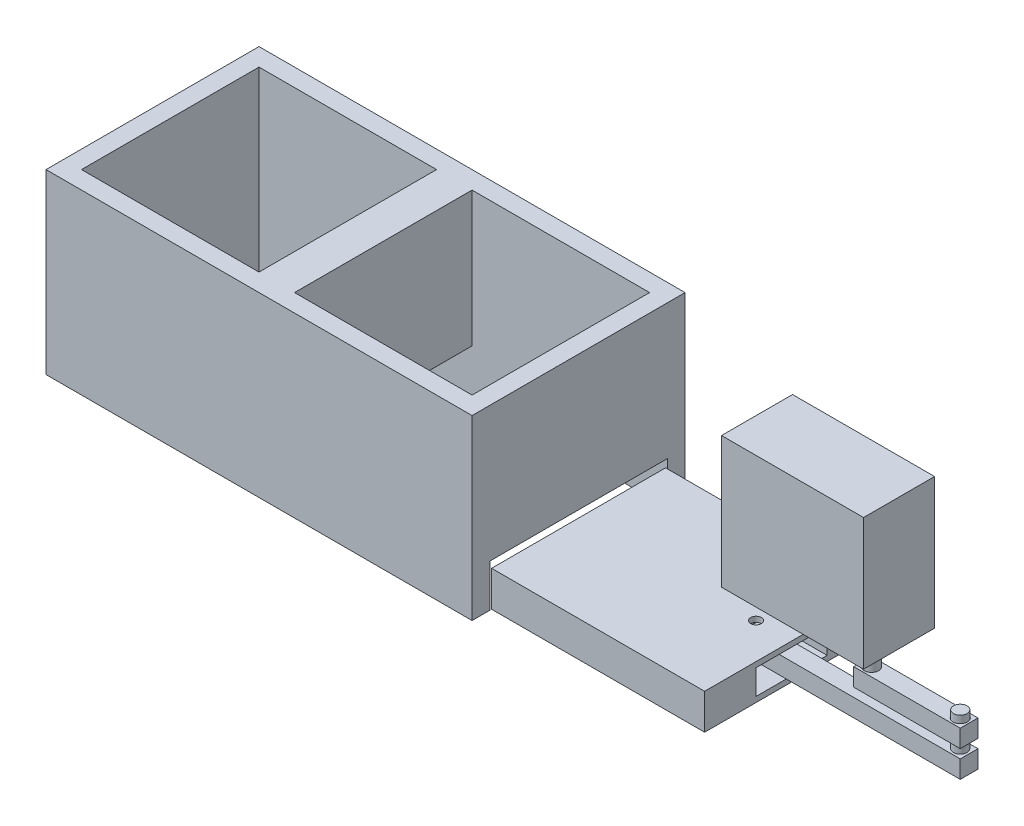
SolidWorks part; units mm, degrees
ref_plane "前视基准面" through (0, 0, 0) normal (0, 0, 1) x (1, 0, 0)
ref_plane "上视基准面" through (0, 0, 0) normal (0, 1, 0) x (1, 0, 0)
ref_plane "右视基准面" through (0, 0, 0) normal (1, 0, 0) x (0, 0, -1)
sketch "草图1" plane through (0, 0, 0) normal (0, 1, 0) x (1, 0, 0)
  line L1 (-30, 30) -> (30, 30)
  line L2 (-30, 30) -> (-30, -30)
  line L3 (-30, -30) -> (30, -30)
  line L4 (30, 30) -> (30, -30)
  dimension "D1" = 30
  dimension "D2" = 30
  dimension "D3" = 30
  dimension "D4" = 30
extrude "凸台-拉伸1" add sketch "草图1" along normal blind 50
sketch "草图2" plane through (0, 0, 0) normal (0, -1, 0) x (1, 0, 0)
  line L1 (25, 25) -> (-25, 25)
  line L2 (25, 25) -> (25, -25)
  line L3 (25, -25) -> (-25, -25)
  line L4 (-25, 25) -> (-25, -25)
  dimension "D1" = 25
  dimension "D2" = 25
  dimension "D3" = 25
  dimension "D4" = 25
extrude "切除-拉伸1" cut sketch "草图2" against normal through all
sketch "草图3" plane through (30, 0, 0) normal (1, 0, 0) x (0, 0, -1)
  line L0 (-30, 0) -> (30, 0) construction
  line L1 (25, 0) -> (-25, 0)
  line L2 (25, 0) -> (25, 12)
  line L3 (25, 12) -> (-25, 12)
  line L4 (-25, 0) -> (-25, 12)
  dimension "D1" = 12
  dimension "D2" = 25
  dimension "D3" = 25
extrude "切除-拉伸2" cut sketch "草图3" against normal blind 10
mirror "镜向3" about plane through (30, 50, -30) normal (-1, 0, 0) of "切除-拉伸2", "切除-拉伸1", "凸台-拉伸1"
sketch "草图4" plane through (90, 0, 0) normal (1, 0, 0) x (0, 0, -1)
  line L0 (30, 0) -> (-30, 0) construction
  line L1 (25, 0) -> (-25, 0)
  line L2 (25, 0) -> (25, 12)
  line L3 (25, 12) -> (-25, 12)
  line L4 (-25, 0) -> (-25, 12)
  point P6 (0, 12)
  dimension "D1" = 12
  dimension "D2" = 25
  dimension "D3" = 25
extrude "切除-拉伸3" cut sketch "草图4" against normal blind 10
sketch "草图6" plane through (0, 0, 0) normal (0, -1, 0) x (1, 0, 0)
  line L0 (85, -25) -> (90, -25) construction
  line L1 (150, -24.5) -> (90, -24.5)
  line L2 (150, -24.5) -> (150, 25.5)
  line L3 (150, 25.5) -> (90, 25.5)
  line L4 (90, -24.5) -> (90, 25.5)
  line L5 (90, 25) -> (-25, 25) construction
  line L6 (90, -25) -> (90, 25) construction
  point P6 (87.5, -25)
  point P7 (120, 25.5)
  point P12 (90, 0.5)
  dimension "D1" = 0.5
  dimension "D2" = 0.5
  dimension "D3" = 0
  dimension "D4" = 60
extrude "凸台-拉伸2" add sketch "草图6" against normal blind 10
sketch "草图8" plane through (150, 0, 0) normal (1, 0, 0) x (0, 0, -1)
  line L0 (24.5, 10) -> (-25.5, 10) construction
  line L1 (-24.5, 10) -> (-25.5, 10)
  line L2 (-24.5, 10) -> (-24.5, 0)
  line L3 (-24.5, 0) -> (-25.5, 0)
  line L4 (-25.5, 10) -> (-25.5, 0)
  line L5 (-25.5, 10) -> (-25.5, 0) construction
  line L6 (-25.5, 10) -> (-25.5, 0) construction
  line L7 (-25, 12) -> (-25, 10) construction
  dimension "D1" = 0.5
extrude "切除-拉伸5" cut sketch "草图8" against normal blind 60
sketch "草图13" plane through (150, 0, 0) normal (1, 0, 0) x (0, 0, -1)
  line L0 (24.5, 0) -> (-24.5, 0) construction
  line L1 (-7, 8.5) -> (7, 8.5)
  line L2 (-7, 8.5) -> (-7, 1.5)
  line L3 (-7, 1.5) -> (7, 1.5)
  line L4 (7, 8.5) -> (7, 1.5)
  dimension "D1" = 7
  dimension "D2" = 7
  dimension "D3" = 7
  dimension "D4" = 1.5
extrude "切除-拉伸6" cut sketch "草图13" against normal blind 12
sketch "草图14" plane through (138, 0, 0) normal (1, 0, 0) x (0, 0, -1)
  line L0 (-7, 1.5) -> (7, 1.5) construction
  line L1 (-2.5, 7.5) -> (2.5, 7.5)
  line L2 (-2.5, 7.5) -> (-2.5, 2.5)
  line L3 (-2.5, 2.5) -> (2.5, 2.5)
  line L4 (2.5, 7.5) -> (2.5, 2.5)
  line L5 (7, 1.5) -> (7, 8.5) construction
  point P4 (-2.5, 5)
  point P7 (2.5, 5)
  dimension "D1" = 5
  dimension "D2" = 5
  dimension "D3" = 1
  dimension "D4" = 4.5
extrude "凸台-拉伸4" add sketch "草图14" along normal blind 62
sketch "草图15" plane through (150, 0, 0) normal (1, 0, 0) x (0, 0, -1)
  line L1 (-7, 8.5) -> (-10, 8.5)
  line L2 (-7, 8.5) -> (-7, 1.5)
  line L3 (-7, 1.5) -> (-10, 1.5)
  line L4 (-10, 8.5) -> (-10, 1.5)
  line L6 (24.5, 0) -> (-24.5, 0) construction
  dimension "D1" = 3
  dimension "D2" = 1.5
extrude "切除-拉伸7" cut sketch "草图15" against normal blind 12
sketch "草图16" plane through (150, 0, 0) normal (1, 0, 0) x (0, 0, -1)
  line L1 (7, 8.5) -> (10, 8.5)
  line L2 (7, 8.5) -> (7, 1.5)
  line L3 (7, 1.5) -> (10, 1.5)
  line L4 (10, 8.5) -> (10, 1.5)
  dimension "D1" = 3
extrude "切除-拉伸8" cut sketch "草图16" against normal blind 12
sketch "草图18" plane through (0, 10, 0) normal (0, 1, 0) x (1, 0, 0)
  line L0 (200, 2.5) -> (138, 2.5) construction
  line L1 (170, 2.5) -> (200, 2.5)
  line L2 (170, 2.5) -> (170, -2.5)
  line L3 (170, -2.5) -> (200, -2.5)
  line L4 (200, 2.5) -> (200, -2.5)
  line L5 (200, -2.5) -> (138, -2.5) construction
  point P8 (200, 0)
  dimension "D1" = 30
extrude "凸台-拉伸5" add sketch "草图18" along normal blind 5 separate body
sketch "草图19" plane through (0, 15, 0) normal (0, 1, 0) x (1, 0, 0)
  line L0 (170, -2.5) -> (200, -2.5) construction
  line L1 (200, -2.5) -> (200, 2.5) construction
  circle A0 centre (197.5, 0) radius 2.0025
  dimension "D1" = 2.5
  dimension "D2" = 2.5
extrude "切除-拉伸9" cut sketch "草图19" against normal blind 5
sketch "草图20" plane through (0, 10, 0) normal (0, 1, 0) x (1, 0, 0)
  line L0 (200, 2.5) -> (138, 2.5) construction
  line L1 (150, 24.5) -> (150, -24.5) construction
  circle A0 centre (140, 0) radius 1.5
  dimension "D1" = 2.5
  dimension "D2" = 10
extrude "切除-拉伸10" cut sketch "草图20" against normal through all both and the other way through all
sketch "草图21" plane through (0, 15, 0) normal (0, 1, 0) x (1, 0, 0)
  circle A0 centre (197.5, 0) radius 1.9046
  circle A1 centre (197.5, 0) radius 2.0025 construction
  dimension "D1" = 0
extrude "凸台-拉伸6" add sketch "草图21" against normal blind 8 and the other way blind 2
sketch "草图22" plane through (0, 15, 0) normal (0, 1, 0) x (1, 0, 0)
  line L0 (170, -2.5) -> (200, -2.5) construction
  line L1 (170, 2.5) -> (170, -2.5) construction
  circle A0 centre (172.5, 0) radius 2
  dimension "D1" = 2.5
  dimension "D2" = 2.5
extrude "凸台-拉伸7" add sketch "草图22" along normal blind 8
sketch "草图23" plane through (0, 23, 0) normal (0, 1, 0) x (1, 0, 0)
  line L0 (150, 24.5) -> (150, -24.5) construction
  line L1 (140, 10.2658) -> (180, 10.2658)
  line L2 (140, 10.2658) -> (140, -9.7342)
  line L3 (140, -9.7342) -> (180, -9.7342)
  line L4 (180, 10.2658) -> (180, -9.7342)
  dimension "D1" = 40
  dimension "D2" = 20
  dimension "D3" = 10
extrude "凸台-拉伸8" add sketch "草图23" along normal blind 37
